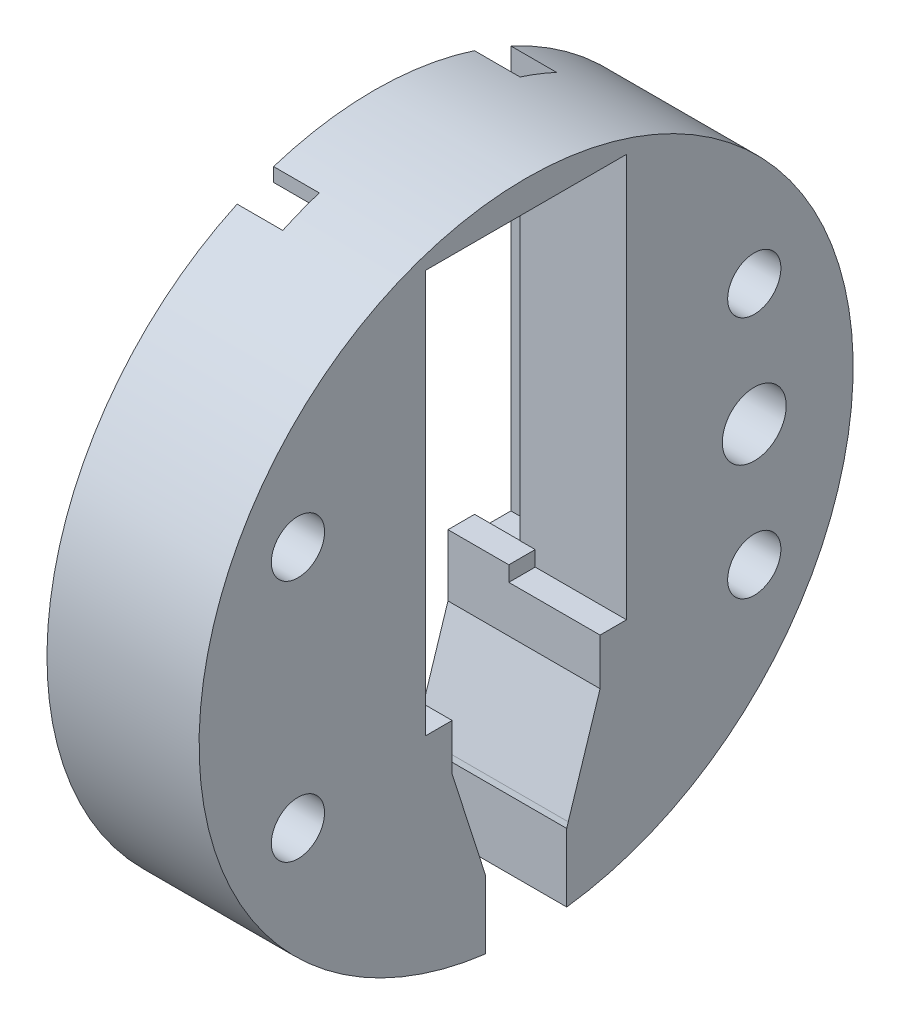
SolidWorks part; units mm, degrees
material "Zoltek Panex 33"
ref_plane "Front Plane" through (0, 0, 0) normal (0, 0, 1) x (1, 0, 0)
ref_plane "Top Plane" through (0, 0, 0) normal (0, 1, 0) x (1, 0, 0)
ref_plane "Right Plane" through (0, 0, 0) normal (1, 0, 0) x (0, 0, -1)
sketch "Sketch1" plane through (0, 0, 0) normal (1, 0, 0) x (0, 0, -1)
  circle A0 centre (0, 0) radius 21.5
  dimension "D1" = 43
extrude "Boss-Extrude1" add sketch "Sketch1" along normal blind 10
sketch "Sketch13" plane through (0, 0, 0) normal (1, 0, 0) x (0, 0, -1)
  line L0 (-2.6704, -16.8582) -> (-2.7704, -16.5304)
  line L1 (6.6, 19.5569) -> (6.6, -6.9431)
  line L2 (-6.6, 19.5569) -> (-6.6, -6.9431)
  line L3 (0, -25.25) -> (0, 0) construction
  line L4 (2.6704, -16.8582) -> (2.7704, -16.5304)
  line L5 (-4.8624, -10) -> (-2.7704, -16.5304)
  line L6 (0, -25.25) -> (-1.0006, -21.9772)
  line L7 (-6.6, 19.5569) -> (6.6, 19.5569)
  line L8 (-6.6, -6.9431) -> (-4.8624, -6.9431)
  line L9 (6.6, -6.9431) -> (4.8624, -6.9431)
  line L10 (1.0006, -21.9772) -> (0, -25.25)
  line L11 (4.8624, -10) -> (2.7704, -16.5304)
  line L12 (-2.6704, -16.8582) -> (-2.6704, -21.8373)
  line L13 (-4.8624, -10) -> (-4.8624, -6.9431)
  line L14 (4.8624, -10) -> (4.8624, -6.9431)
  line L15 (2.6704, -16.8582) -> (2.6704, -21.8373)
  arc A0 (-2.6704, -21.8373) -> (-1.0006, -21.9772) centre (0, 0) ccw
  arc A1 (1.0006, -21.9772) -> (2.6704, -21.8373) centre (0, 0) ccw
  dimension "D1" = 13.2
  dimension "D2" = 26.5
  dimension "D3" = 3.0569
  dimension "D4" = 25.25
  dimension "D5" = 6.6
extrude "Cut-Extrude2" cut sketch "Sketch13" along normal up to surface (10 mm away) contours L1 L9 L14 L11 L4 L15 A1 L10 L6 A0 L12 L0 L5 L13 L8 L2 L7 up to face at (10, 0, -21.5)
sketch "Sketch15" plane through (0, 0, 0) normal (-1, 0, 0) x (0, 0, 1)
  line L0 (9, 17.1749) -> (9, -6.9431)
  line L1 (9, 17.1749) -> (-9, 17.1749)
  line L2 (9, -6.9431) -> (-9, -6.9431)
  line L3 (0, -6.9431) -> (0, 17.1749) construction
  line L4 (-9, -6.9431) -> (-9, 17.1749)
  line L5 (-6.6, -6.9431) -> (-4.8624, -6.9431) construction
  point P4 (0, -6.9431)
  point P7 (0, 17.1749)
  dimension "D1" = 18
  dimension "D2" = 24.118
extrude "Cut-Extrude3" cut sketch "Sketch15" against normal blind 3
sketch "Sketch17" plane through (0, -6.9431, 0) normal (0, 1, 0) x (1, 0, 0)
  line L0 (0, 4.8624) -> (0, 6.6124)
  line L1 (0, 9) -> (0, 4.8624) construction
  line L2 (0, 6.6124) -> (4, 6.6124)
  line L3 (4, 6.6124) -> (4, 4.8624)
  line L4 (10, 4.8624) -> (0, 4.8624) construction
  line L5 (4, 4.8624) -> (0, 4.8624)
  dimension "D1" = 1.75
  dimension "D2" = 4
extrude "Boss-Extrude3" add sketch "Sketch17" along normal blind 1
sketch "Sketch18" plane through (0, -6.9431, 0) normal (0, 1, 0) x (1, 0, 0)
  line L0 (10, -6.6) -> (3, -6.6) construction
  line L1 (0, -4.8624) -> (6.5, -4.8624)
  line L2 (0, -4.8624) -> (0, -6.6)
  line L3 (0, -6.6) -> (6.5, -6.6)
  line L4 (6.5, -4.8624) -> (6.5, -6.6)
  dimension "D1" = 1.7376
extrude "Boss-Extrude4" add sketch "Sketch18" along normal blind 1
sketch "Sketch19" plane through (0, 0, 0) normal (1, 0, 0) x (0, 0, -1)
  line L0 (-11, 28.9371) -> (-11, -33.8532)
  line L1 (11, 28.9371) -> (11, -33.8532)
  line L2 (-11, 28.9371) -> (11, 28.9371)
  line L3 (-11, -33.8532) -> (11, -33.8532)
  dimension "D1" = 22
  dimension "D2" = 11
sketch "Sketch39" plane through (0, 0, 0) normal (1, 0, 0) x (0, 0, -1)
  line L0 (9, 17.1749) -> (9, -6.9431) construction
  line L1 (6.6, 17.1749) -> (9, 17.1749)
  line L2 (6.6, 17.1749) -> (6.6, 21.3015)
  line L3 (6.6, 21.3015) -> (9, 21.3015)
  line L4 (9, 17.1749) -> (9, 21.3015)
  line L5 (-6.6, 17.1749) -> (-9, 17.1749)
  line L6 (-6.6, 17.1749) -> (-6.6, 21.3015)
  line L7 (-6.6, 21.3015) -> (-9, 21.3015)
  line L8 (-9, 17.1749) -> (-9, 21.3015)
  line L9 (-9, -6.9431) -> (-9, 17.1749) construction
extrude "Cut-Extrude7" cut sketch "Sketch39" along normal blind 3 from surface at 0 starting at face at (0, -1.3792, -0.0011)
sketch "Sketch41" plane through (0, 0, 0) normal (-1, 0, 0) x (0, 0, 1)
  line L0 (0, 0) -> (0, 12.1361) construction
  line L1 (0.7617, 0) -> (-23.5675, 0) construction
  line L2 (-15, 8) -> (-15, -8) construction
  circle A3 centre (-15, 8) radius 1.75
  circle A4 centre (15, 8) radius 1.75
  circle A5 centre (15, -8) radius 1.75
  circle A6 centre (-15, -8) radius 1.75
  circle A8 centre (-15, 0) radius 2.1
  dimension "D1" = 8
  dimension "D2" = 15
  dimension "D3" = 3.5
extrude "Cut-Extrude8" cut sketch "Sketch41" against normal through all
